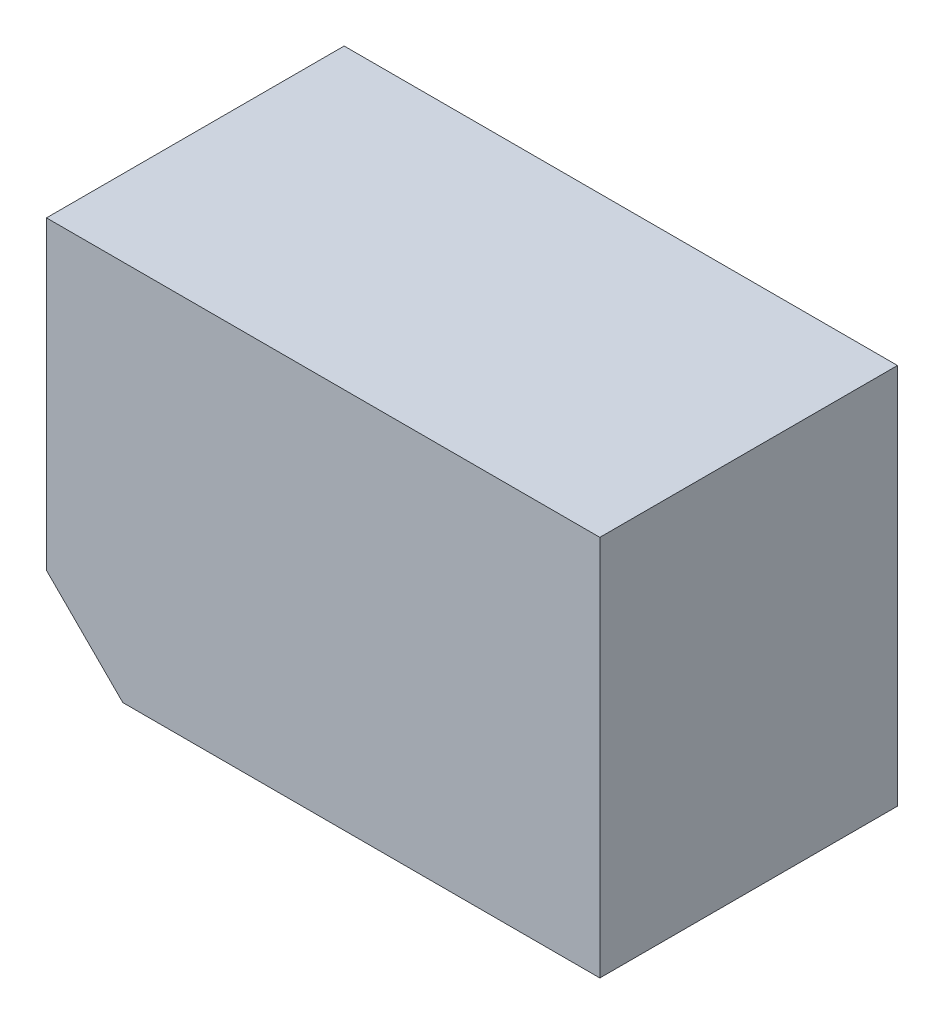
SolidWorks part; units mm, degrees
material "Pine"
ref_plane "Front Plane" through (0, 0, 0) normal (0, 0, 1) x (1, 0, 0)
ref_plane "Top Plane" through (0, 0, 0) normal (0, 1, 0) x (1, 0, 0)
ref_plane "Right Plane" through (0, 0, 0) normal (1, 0, 0) x (0, 0, -1)
sketch "Sketch1" plane through (0, 0, 0) normal (0, 0, 1) x (1, 0, 0)
  line L0 (-125, -100) -> (-145, -80)
  line L1 (0, 0) -> (-145, 0)
  line L2 (0, 0) -> (0, -100)
  line L3 (0, -100) -> (-125, -100)
  line L4 (-145, 0) -> (-145, -80)
  point P1 (-145, -100)
  dimension "D1" = 100
  dimension "D2" = 145
extrude "Boss-Extrude1" add sketch "Sketch1" along normal blind 78
